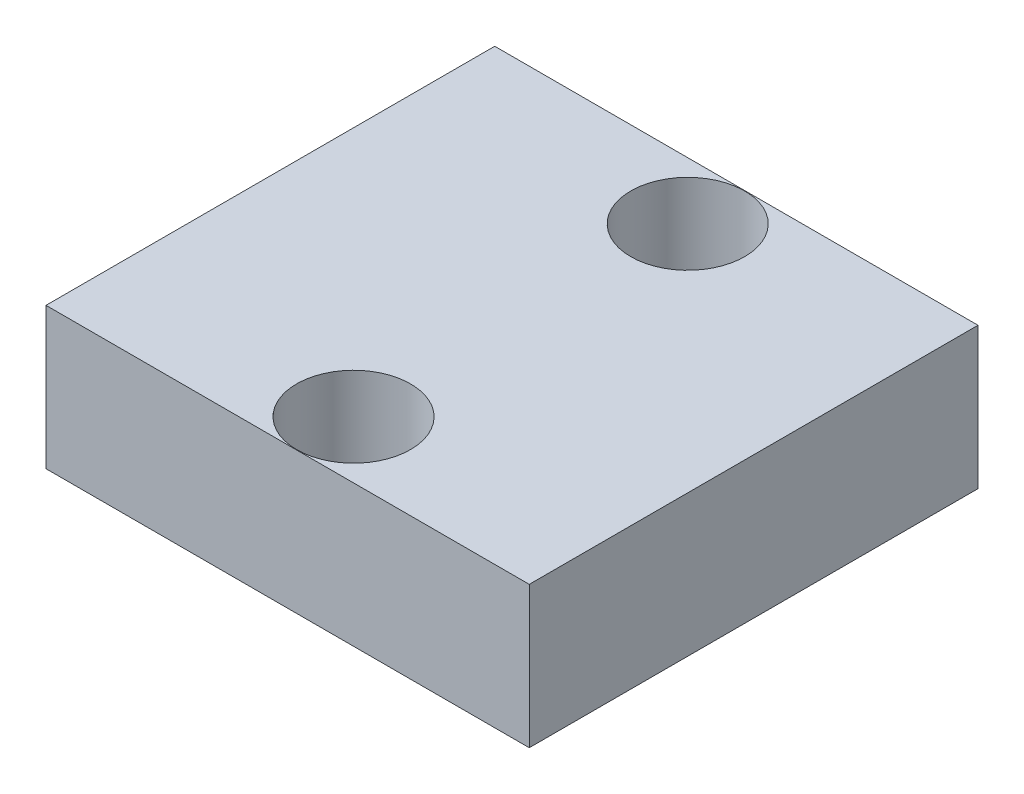
SolidWorks part; units mm, degrees
ref_plane "Front Plane" through (0, 0, 0) normal (0, 0, 1) x (1, 0, 0)
ref_plane "Top Plane" through (0, 0, 0) normal (0, 1, 0) x (1, 0, 0)
ref_plane "Right Plane" through (0, 0, 0) normal (1, 0, 0) x (0, 0, -1)
sketch "Sketch1" plane through (0, 0, 0) normal (0, 1, 0) x (1, 0, 0)
  line L1 (-7, -6.5) -> (7, -6.5)
  line L2 (-7, -6.5) -> (-7, 6.5)
  line L3 (-7, 6.5) -> (7, 6.5)
  line L4 (7, -6.5) -> (7, 6.5)
  line L5 (-7, -6.5) -> (7, 6.5) construction
  line L6 (-7, 6.5) -> (7, -6.5) construction
  circle A0 centre (0.25, 4.84) radius 1.65
  circle A1 centre (0.25, -4.84) radius 1.65
  point P0 (0, 0)
  dimension "D3" = 3.3
  dimension "D1" = 14
  dimension "D2" = 13
  dimension "D4" = 6.75
  dimension "D5" = 1.66
  dimension "D6" = 1.66
extrude "Boss-Extrude3" add sketch "Sketch1" along normal blind 4.1
sketch "Sketch2" plane through (7, 0, 0) normal (1, 0, 0) x (0, 0, -1)
  circle A0 centre (0.6404, 1.5096) radius 1.7708
